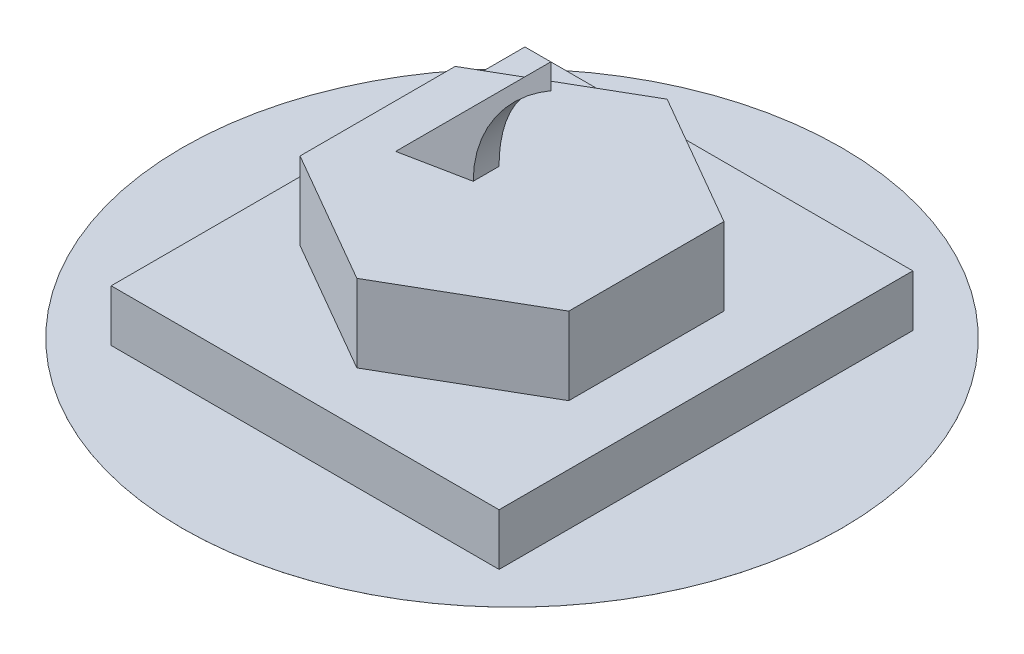
SolidWorks part; units mm, degrees
ref_plane "Front Plane" through (0, 0, 0) normal (0, 0, 1) x (1, 0, 0)
ref_plane "Top Plane" through (0, 0, 0) normal (0, 1, 0) x (1, 0, 0)
ref_plane "Right Plane" through (0, 0, 0) normal (1, 0, 0) x (0, 0, -1)
sketch "Sketch1" plane through (0, 0, 0) normal (0, 1, 0) x (1, 0, 0)
  line L1 (0, 0) -> (150, 0)
  line L2 (0, 0) -> (0, 160)
  line L3 (0, 160) -> (150, 160)
  line L4 (150, 0) -> (150, 160)
  dimension "D1" = 150
  dimension "D2" = 160
extrude "Extrude1" add sketch "Sketch1" along normal blind 20
sketch "Sketch2" plane through (0, 20, 0) normal (0, 1, 0) x (1, 0, 0)
  line L0 (150, 160) -> (0, 0) construction
  line L1 (75, 80) -> (75, 140) construction
  line L2 (75, 140) -> (23.0385, 110)
  line L3 (23.0385, 110) -> (23.0385, 50)
  line L4 (23.0385, 50) -> (75, 20)
  line L5 (75, 20) -> (126.9615, 50)
  line L6 (126.9615, 50) -> (126.9615, 110)
  line L7 (126.9615, 110) -> (75, 140)
  circle A0 centre (75, 80) radius 51.9615 construction
  dimension "D1" = 60
extrude "Extrude2" add sketch "Sketch2" along normal blind 30
sketch "Sketch3" plane through (0, 50, 0) normal (0, 1, 0) x (1, 0, 0)
  line L0 (126.9615, 80) -> (23.0385, 80) construction
  line L1 (126.9615, 50) -> (126.9615, 110) construction
  line L2 (23.0385, 110) -> (23.0385, 50) construction
  line L3 (75, 140) -> (75, 20) construction
  line L4 (40, 90) -> (40, 70)
  line L5 (40, 70) -> (90, 80)
  line L6 (90, 80) -> (40, 90)
  line L7 (0, 160) -> (0, 0) construction
  dimension "D1" = 40
  dimension "D2" = 20
  dimension "D3" = 10
  dimension "D4" = 50
extrude "Extrude3" add sketch "Sketch3" along normal blind 50
sketch "Sketch4" plane through (0, 0, 0) normal (0, 0, 1) x (1, 0, 0)
  line L0 (75, 50) -> (126.9615, 50) construction
  line L1 (110, 95) -> (110, 50)
  line L2 (110, 50) -> (65, 50)
  line L3 (90, 100) -> (90, 50) construction
  line L4 (40, 50) -> (90, 100)
  line L5 (40, 100) -> (90, 100) construction
  line L6 (90, 100) -> (40, 100)
  line L7 (40, 100) -> (40, 50)
  arc A0 (110, 95) -> (65, 50) centre (110, 50) ccw
  dimension "D1" = 45
  dimension "D2" = 20
  dimension "D3" = 50
extrude "Extrude4" cut sketch "Sketch4" against normal through all
sketch "Sketch5" plane through (0, 0, 0) normal (0, 1, 0) x (1, 0, 0)
  line L0 (150, 160) -> (0, 0) construction
  circle A0 centre (75, 80) radius 127.5
  dimension "D1" = 255
extrude "Extrude5" add sketch "Sketch5" along normal blind 0.01
